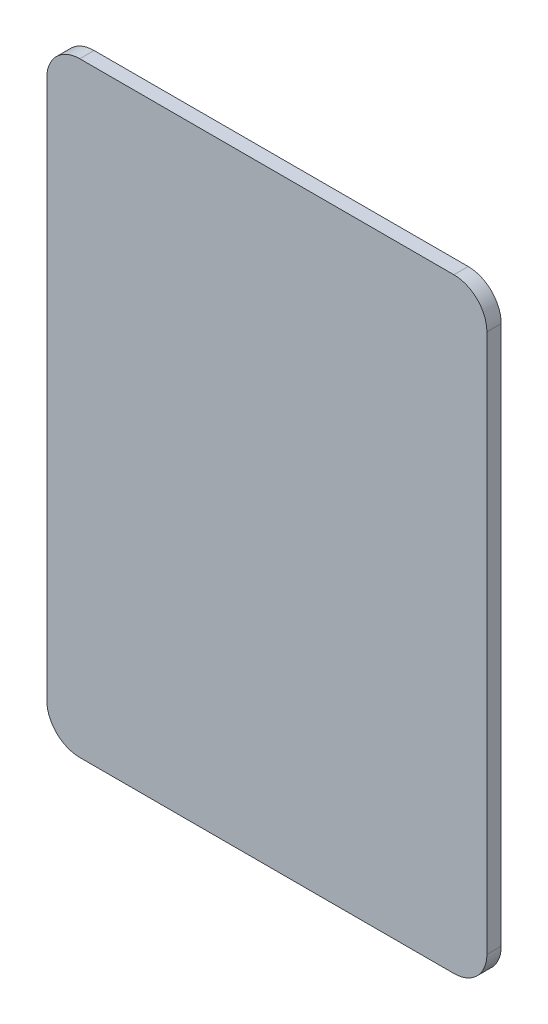
SolidWorks part; units mm, degrees
ref_plane "Front Plane" through (0, 0, 0) normal (1, 0, 0) x (0, 1, 0)
ref_plane "Top Plane" through (0, 0, 0) normal (0, 0, 1) x (0, 1, 0)
ref_plane "Right Plane" through (0, 0, 0) normal (0, 1, 0) x (-1, 0, 0)
sketch "Sketch1" plane through (0, 0, 0) normal (0, 0, 1) x (0, 1, 0)
  line L1 (-27.5, -20) -> (27.5, -20)
  line L2 (-27.5, -20) -> (-27.5, 20)
  line L3 (-27.5, 20) -> (27.5, 20)
  line L4 (27.5, -20) -> (27.5, 20)
  line L5 (-27.5, -20) -> (27.5, 20) construction
  line L6 (-27.5, 20) -> (27.5, -20) construction
  point P0 (0, 0)
  dimension "D1" = 55
  dimension "D2" = 40
extrude "Boss-Extrude1" add sketch "Sketch1" along normal blind 1.3
fillet "Fillet1" radius 3 4 edges at (-20, 27.5, 0.65) (-20, -27.5, 0.65) (20, 27.5, 0.65) (20, -27.5, 0.65)
